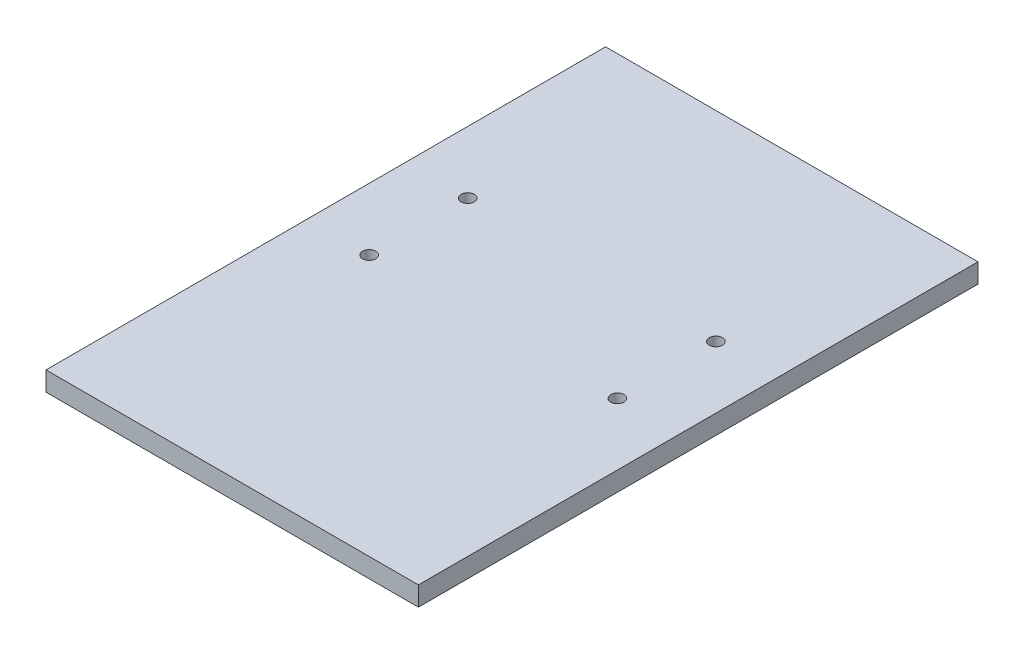
SolidWorks part; units mm, degrees
other "Markup1"
sketch "Sketch5" plane through (-120.015, 12.7, 180.34) normal (-0.0435, 0.9946, 0.0939) x (0.9888, 0.0294, 0.1461)
ref_plane "Front Plane" through (0, 0, 0) normal (0, 0, 1) x (1, 0, 0)
ref_plane "Top Plane" through (0, 0, 0) normal (0, 1, 0) x (1, 0, 0)
ref_plane "Right Plane" through (0, 0, 0) normal (1, 0, 0) x (0, 0, -1)
other "Center of Mass"
sketch "Sketch1" plane through (0, 0, 0) normal (0, 1, 0) x (1, 0, 0)
  line L1 (-120.015, 180.34) -> (120.015, 180.34)
  line L2 (-120.015, 180.34) -> (-120.015, -180.34)
  line L3 (-120.015, -180.34) -> (120.015, -180.34)
  line L4 (120.015, 180.34) -> (120.015, -180.34)
  line L5 (-120.015, 180.34) -> (120.015, -180.34) construction
  line L6 (-120.015, -180.34) -> (120.015, 180.34) construction
  point P0 (0, 0)
extrude "Boss-Extrude1" add sketch "Sketch1" along normal blind 12.446
sketch "Sketch2" plane through (0, 12.446, 0) normal (0, 1, 0) x (1, 0, 0)
  line L1 (-120.015, 180.34) -> (120.015, 180.34)
  line L2 (-120.015, 180.34) -> (-120.015, -180.34)
  line L3 (-120.015, -180.34) -> (120.015, -180.34)
  line L4 (120.015, 180.34) -> (120.015, -180.34)
  line L5 (-120.015, 180.34) -> (120.015, -180.34) construction
  line L6 (-120.015, -180.34) -> (120.015, 180.34) construction
  line L11 (67.31, 76.835) -> (92.71, 76.835)
  line L12 (67.31, 76.835) -> (67.31, -180.34)
  line L13 (67.31, -180.34) -> (92.71, -180.34)
  line L14 (92.71, 76.835) -> (92.71, -180.34)
  line L15 (67.31, 76.835) -> (92.71, -180.34) construction
  line L16 (67.31, -180.34) -> (92.71, 76.835) construction
  circle A0 centre (80.01, 51.435) radius 2.54
  circle A1 centre (80.01, -12.065) radius 2.54
  point P0 (0, 0)
  point P7 (80.01, -51.7525)
  dimension "D2" = 63.5
  dimension "D1" = 80.01
  dimension "D3" = 25.4
  dimension "D4" = 257.175
hole_wizard "M10x1.5 Tapped Hole1" positions "Sketch3" profile "Sketch4" tap size "M10x1.5" standard "ANSI Metric" end condition through all
sketch "Sketch3" plane through (0, 12.446, 0) normal (0, 1, 0) x (1, 0, 0)
  point P0 (80.01, 51.435)
  point P3 (80.01, -12.065)
sketch "Sketch4" plane through (80.01, 12.446, -51.435) normal (1, 0, 0) x (0, 0, 1)
  line L0 (0, 0) -> (0, 12.446)
  line L1 (0, 12.446) -> (4.25, 12.446)
  line L2 (4.25, 12.446) -> (4.25, 0)
  line L5 (4.25, 0) -> (0, 0)
  line L11 (0, -6.35) -> (0, 107.95) construction
  dimension "Thru Tap Drill Dia." = 8.5
  dimension "Thru Tap Drill Depth" = 12.446
ref_plane "Plane1" through (0, 0, 0) normal (-1, 0, 0) x (0, 0, 1)
mirror "Mirror1" about plane through (0, 0, 0) normal (-1, 0, 0) of "M10x1.5 Tapped Hole1"
